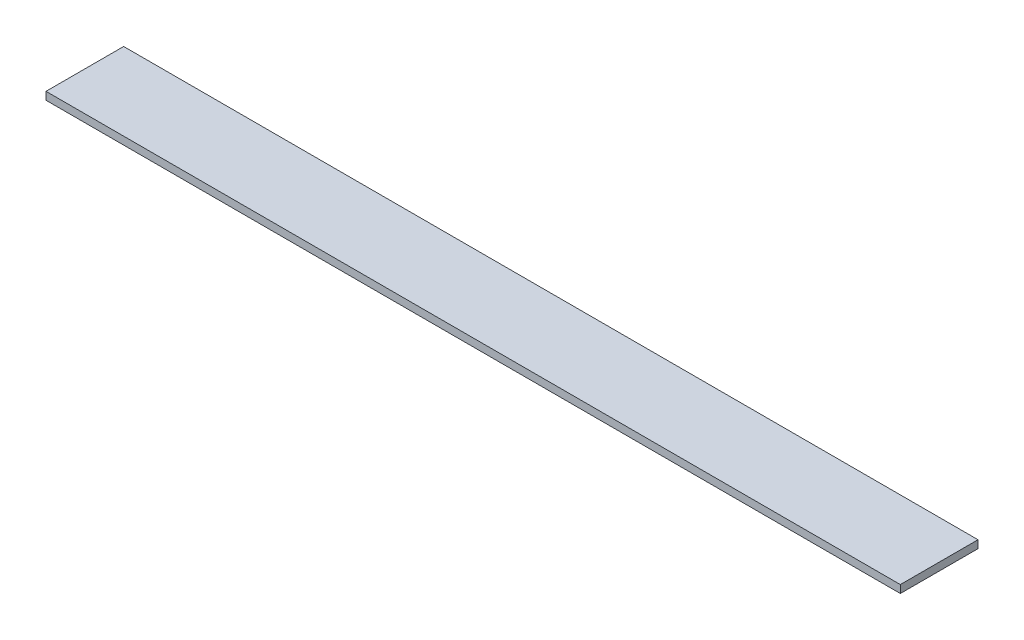
SolidWorks part; units mm, degrees
ref_plane "Face" through (0, 0, 0) normal (0, 0, 1) x (1, 0, 0)
ref_plane "Dessus" through (0, 0, 0) normal (0, 1, 0) x (1, 0, 0)
ref_plane "Droite" through (0, 0, 0) normal (1, 0, 0) x (0, 0, -1)
sketch "Esquisse1" plane through (0, 0, 0) normal (0, 1, 0) x (1, 0, 0)
  line L1 (0, 0) -> (1100, 0)
  line L2 (0, 0) -> (0, 100)
  line L3 (0, 100) -> (1100, 100)
  line L4 (1100, 0) -> (1100, 100)
  dimension "D1" = 1100
  dimension "D2" = 100
extrude "Extrusion1" add sketch "Esquisse1" along normal blind 10
